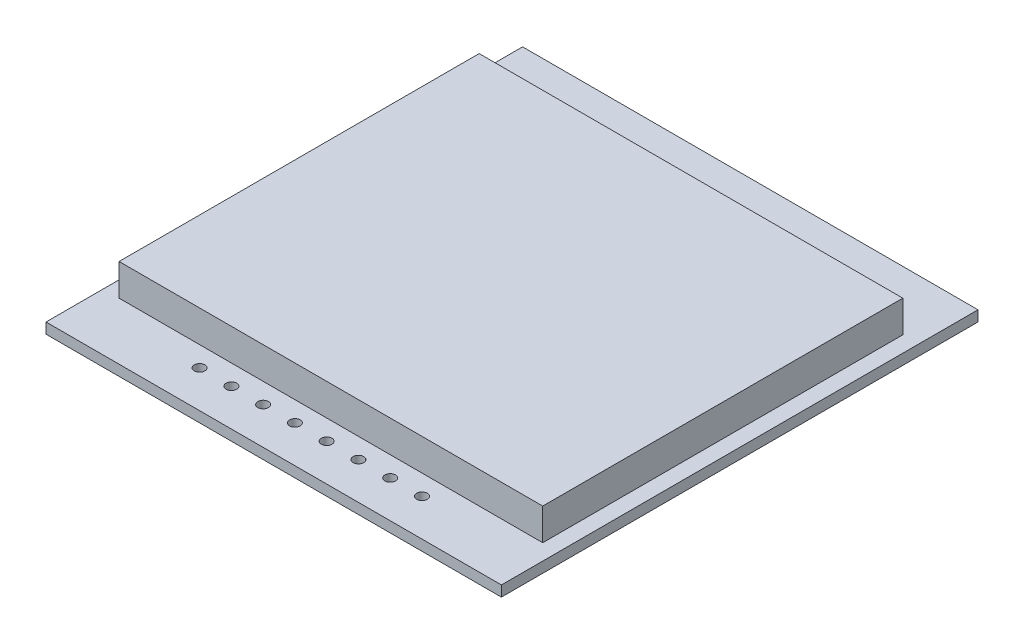
SolidWorks part; units mm, degrees
ref_plane "Alzado" through (0, 0, 0) normal (0, 0, 1) x (1, 0, 0)
ref_plane "Planta" through (0, 0, 0) normal (0, 1, 0) x (1, 0, 0)
ref_plane "Vista lateral" through (0, 0, 0) normal (1, 0, 0) x (0, 0, -1)
sketch "Croquis1" plane through (0, 0, 0) normal (0, 1, 0) x (1, 0, 0)
  line L1 (-21.5, -22.5) -> (21.5, -22.5)
  line L2 (-21.5, -22.5) -> (-21.5, 22.5)
  line L3 (-21.5, 22.5) -> (21.5, 22.5)
  line L4 (21.5, -22.5) -> (21.5, 22.5)
  line L5 (-21.5, -22.5) -> (21.5, 22.5) construction
  line L6 (-21.5, 22.5) -> (21.5, -22.5) construction
  point P0 (0, 0)
  dimension "D1" = 43
  dimension "D2" = 45
extrude "Saliente-Extruir1" add sketch "Croquis1" along normal blind 1
sketch "Croquis2" plane through (0, 1, 0) normal (0, 1, 0) x (1, 0, 0)
  line L0 (0, 0) -> (0, 22.5) construction
  line L1 (21.5, 22.5) -> (-21.5, 22.5) construction
  line L3 (-20, -17.1) -> (20, -17.1)
  line L4 (-20, -17.1) -> (-20, 16.9)
  line L5 (-20, 16.9) -> (20, 16.9)
  line L6 (20, -17.1) -> (20, 16.9)
  line L7 (-20, -17.1) -> (20, 16.9) construction
  line L8 (-20, 16.9) -> (20, -17.1) construction
  point P5 (0, -0.1)
  dimension "D1" = 0.1
  dimension "D2" = 34
  dimension "D3" = 40
extrude "Saliente-Extruir2" add sketch "Croquis2" along normal blind 3
sketch "Croquis3" plane through (0, 1, 0) normal (0, 1, 0) x (1, 0, 0)
  line L0 (0, -17.1) -> (0, -22.5) construction
  line L1 (-20, -17.1) -> (20, -17.1) construction
  line L2 (-21.5, -22.5) -> (21.5, -22.5) construction
  circle A0 centre (1.5, -19) radius 0.5
  circle A1 centre (4.5, -19) radius 0.5
  circle A2 centre (7.5, -19) radius 0.5
  circle A3 centre (10.5, -19) radius 0.5
  circle A4 centre (-10.5, -19) radius 0.5
  circle A5 centre (-7.5, -19) radius 0.5
  circle A6 centre (-4.5, -19) radius 0.5
  circle A7 centre (-1.5, -19) radius 0.5
  dimension "D1" = 1
  dimension "D2" = 3
  dimension "D3" = 3.5
  dimension "D4" = 4
extrude "Cortar-Extruir1" cut sketch "Croquis3" against normal through all
